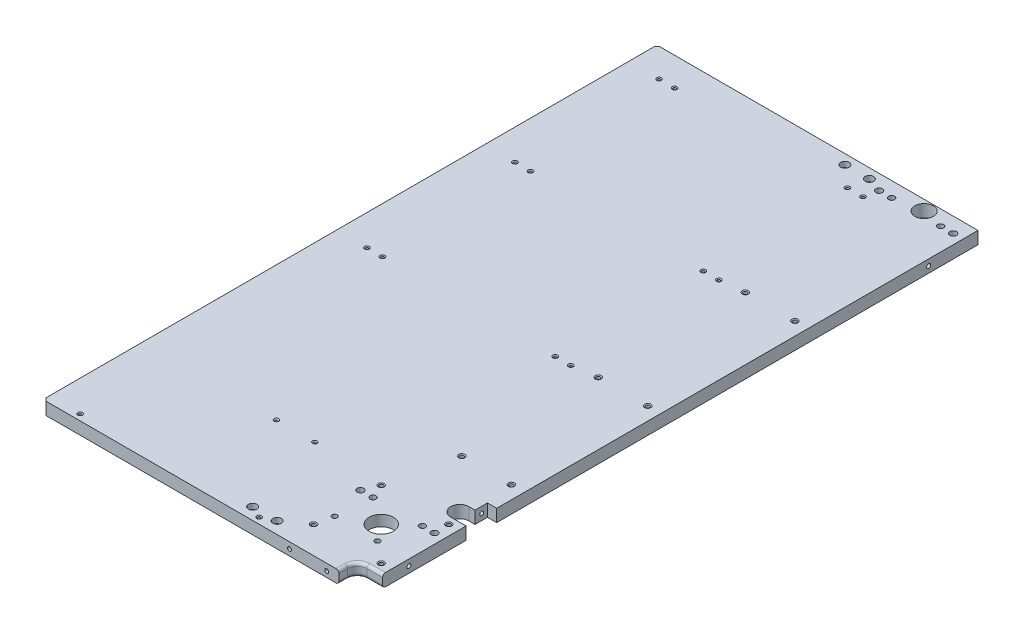
SolidWorks part; units mm, degrees
material "1060 Alloy"
ref_plane "Front Plane" through (0, 0, 0) normal (0, 0, 1) x (1, 0, 0)
ref_plane "Top Plane" through (0, 0, 0) normal (0, 1, 0) x (1, 0, 0)
ref_plane "Right Plane" through (0, 0, 0) normal (1, 0, 0) x (0, 0, -1)
sketch "Sketch1" plane through (0, 0, 0) normal (0, 1, 0) x (1, 0, 0)
  line L1 (0, 632) -> (330.5, 632)
  line L2 (0, 632) -> (0, 0)
  line L3 (0, 0) -> (330.5, 0)
  line L4 (330.5, 632) -> (330.5, 0)
  dimension "D1" = 632
  dimension "D2" = 330.5
extrude "Boss-Extrude1" add sketch "Sketch1" along normal blind 12.8
sketch "Sketch2" plane through (0, 12.8, 0) normal (0, 1, 0) x (-1, 0, 0)
  line L0 (-330.5, 0) -> (-330.5, -632) construction
  line L1 (-330.5, 0) -> (-304.5, 0)
  line L2 (-330.5, 0) -> (-330.5, -19)
  line L3 (-330.5, -19) -> (-314.5, -19)
  line L4 (-304.5, 0) -> (-304.5, -9)
  line L5 (-330.5, -136.5) -> (-320.95, -136.5)
  line L6 (-330.5, -136.5) -> (-330.5, -105)
  line L7 (-330.5, -105) -> (-314.68, -105)
  line L8 (-320.95, -136.5) -> (-320.95, -123.7)
  line L9 (-320.95, -123.7) -> (-314.68, -123.7)
  line L10 (-305.33, -114.35) -> (-305.33, 515.3854) construction
  line L11 (0, 0) -> (-330.5, 0) construction
  arc A0 (-304.5, -9) -> (-314.5, -19) centre (-314.5, -9) cw
  arc A1 (-314.68, -105) -> (-314.68, -123.7) centre (-314.68, -114.35) cw
  dimension "D1" = 10
  dimension "D2" = 19
  dimension "D3" = 26
  dimension "D4" = 31.5
  dimension "D5" = 18.7
  dimension "D6" = 9.55
  dimension "D7" = 25.17
  dimension "D8" = 105
extrude "Cut-Extrude1" cut sketch "Sketch2" against normal through all
fillet "Fillet1" radius 3 6 edges at (304.5, 0, -4.5) (307.4289, 0, -16.0711) (304.5, 12.8, -4.5) (307.4289, 12.8, -16.0711) (322.5, 0, -19) (322.5, 12.8, -19)
sketch "Sketch3" plane through (0, 12.8, 0) normal (0, 1, 0) x (-1, 0, 0)
  line L0 (0, -6.3) -> (-286.561, -6.3) construction
  line L1 (0, -632) -> (0, 0) construction
  line L2 (0, -302) -> (-330.5, -302) construction
  line L3 (0, -454.4) -> (-330.5, -454.4) construction
  line L4 (0, -602.8) -> (-330.5, -602.8) construction
  line L5 (0, 0) -> (-301.5, 0) construction
  line L7 (-31.4, -302) -> (-31.4, -602.8) construction
  line L8 (-47.4, -302) -> (-47.4, -602.8) construction
  line L9 (-225.3, -302) -> (-225.3, -602.8) construction
  line L10 (-241.3, -302) -> (-241.3, -602.8) construction
  line L11 (-330.5, -136.5) -> (-330.5, -632) construction
  circle A0 centre (-31.8, -6.3) radius 1.45
  circle A1 centre (-216.1, -6.3) radius 1.45
  circle A2 centre (-31.4, -302) radius 1.45
  circle A3 centre (-47.4, -302) radius 1.45
  circle A4 centre (-31.4, -454.4) radius 1.45
  circle A5 centre (-47.4, -454.4) radius 1.45
  circle A6 centre (-31.4, -602.8) radius 1.45
  circle A7 centre (-47.4, -602.8) radius 1.45
  circle A8 centre (-225.3, -602.8) radius 1.45
  circle A9 centre (-241.3, -602.8) radius 1.45
  circle A10 centre (-225.3, -454.4) radius 1.45
  circle A11 centre (-241.3, -454.4) radius 1.45
  circle A12 centre (-241.3, -302) radius 1.45
  circle A13 centre (-225.3, -302) radius 1.45
  dimension "D2" = 2.9
  dimension "D1" = 6.3
  dimension "D3" = 31.8
  dimension "D4" = 216.1
  dimension "D5" = 302
  dimension "D6" = 454.4
  dimension "D7" = 602.8
  dimension "D8" = 31.4
  dimension "D9" = 47.4
  dimension "D10" = 225.3
  dimension "D11" = 241.3
extrude "Cut-Extrude2" cut sketch "Sketch3" against normal through all
chamfer "Chamfer1" distance 1 angle 30 28 edges at (31.8, 0, -4.85) (216.1, 0, -4.85) (31.4, 0, -300.55) (47.4, 0, -300.55) (225.3, 0, -300.55) (241.3, 0, -300.55) (241.3, 0, -601.35) (47.4, 0, -601.35) (47.4, 0, -452.95) (31.4, 0, -452.95) (241.3, 0, -452.95) (225.3, 0, -452.95) (31.4, 0, -601.35) (225.3, 0, -601.35) (241.3, 12.8, -601.35) (225.3, 12.8, -601.35) (31.4, 12.8, -601.35) (47.4, 12.8, -601.35) (47.4, 12.8, -300.55) (31.4, 12.8, -452.95) (47.4, 12.8, -452.95) (241.3, 12.8, -452.95) (225.3, 12.8, -452.95) (241.3, 12.8, -300.55) (225.3, 12.8, -300.55) (216.1, 12.8, -4.85) (31.8, 12.8, -4.85) (31.4, 12.8, -300.55)
sketch "Sketch4" plane through (0, 12.8, 0) normal (0, 1, 0) x (-1, 0, 0)
  line L0 (0, -305.5) -> (-330.5, -305.5) construction
  line L1 (0, -632) -> (0, 0) construction
  line L2 (-330.5, -136.5) -> (-330.5, -632) construction
  line L3 (0, -457) -> (-330.5, -457) construction
  line L4 (0, -165.1) -> (-330.5, -165.1) construction
  line L5 (-266, -457) -> (-266, -165.1) construction
  line L6 (-317, -457) -> (-317, -165.1) construction
  line L7 (0, 0) -> (-301.5, 0) construction
  circle A0 centre (-266, -457) radius 2.1
  circle A1 centre (-317, -457) radius 2.1
  circle A2 centre (-266, -305.5) radius 2.1
  circle A3 centre (-317, -305.5) radius 2.1
  circle A4 centre (-266, -165.1) radius 2.1
  circle A5 centre (-317, -165.1) radius 2.1
  dimension "D1" = 4.2
  dimension "D2" = 266
  dimension "D3" = 317
  dimension "D4" = 165.1
  dimension "D5" = 305.5
  dimension "D6" = 457
extrude "Cut-Extrude3" cut sketch "Sketch4" against normal through all
chamfer "Chamfer2" distance 1 angle 30 12 edges at (266, 0, -454.9) (317, 0, -454.9) (266, 0, -303.4) (317, 0, -303.4) (266, 0, -163) (317, 0, -163) (317, 12.8, -163) (266, 12.8, -163) (266, 12.8, -303.4) (317, 12.8, -303.4) (317, 12.8, -454.9) (266, 12.8, -454.9)
sketch "Sketch5" plane through (0, 12.8, 0) normal (0, 1, 0) x (1, 0, 0)
  line L0 (250.5, 28) -> (320.1, 97.6) construction
  line L1 (250.5, 97.6) -> (320.1, 97.6) construction
  line L2 (250.5, 97.6) -> (250.5, 28) construction
  line L3 (250.5, 28) -> (320.1, 28) construction
  line L4 (320.1, 97.6) -> (320.1, 28) construction
  line L5 (0, 0) -> (301.5, 0) construction
  line L7 (0, 632) -> (0, 0) construction
  circle A0 centre (285.3, 62.8) radius 12.5
  circle A1 centre (320.1, 97.6) radius 2.1
  circle A2 centre (320.1, 28) radius 2.1
  circle A3 centre (250.5, 28) radius 2.1
  circle A4 centre (250.5, 97.6) radius 2.1
  dimension "D1" = 25
  dimension "D2" = 4.2
  dimension "D3" = 69.6
  dimension "D4" = 28
  dimension "D5" = 250.5
extrude "Cut-Extrude4" cut sketch "Sketch5" against normal through all
sketch "Sketch6" plane through (0, 0, 0) normal (0, -1, 0) x (1, 0, 0)
  circle A0 centre (285.3, -62.8) radius 36.425
  dimension "D1" = 72.85
extrude "Cut-Extrude5" cut sketch "Sketch6" against normal blind 1.7
chamfer "Chamfer3" distance 1 angle 30 8 edges at (250.5, 0, -25.9) (320.1, 0, -95.5) (250.5, 0, -95.5) (320.1, 0, -25.9) (250.5, 12.8, -25.9) (320.1, 12.8, -25.9) (320.1, 12.8, -95.5) (250.5, 12.8, -95.5)
sketch "Sketch7" plane through (0, 12.8, 0) normal (0, 1, 0) x (1, 0, 0)
  line L0 (254.2, 45.9) -> (330.5, 45.9) construction
  line L1 (330.5, 22) -> (330.5, 105) construction
  line L2 (0, 0) -> (301.5, 0) construction
  line L3 (0, 632) -> (0, 0) construction
  line L4 (330.5, 82.5) -> (0, 82.5) construction
  circle A0 centre (254.2, 45.9) radius 2.7
  circle A1 centre (298.4, 45.9) radius 2.7
  circle A2 centre (308, 82.5) radius 3.1
  circle A3 centre (257.2, 82.5) radius 3.1
  circle A4 centre (320.5, 82.5) radius 3.425
  circle A5 centre (244.2, 82.5) radius 3.425
  dimension "D4" = 5.4
  dimension "D7" = 6.2
  dimension "D8" = 6.85
  dimension "D1" = 45.9
  dimension "D2" = 254.2
  dimension "D3" = 298.4
  dimension "D5" = 257.2
  dimension "D6" = 82.5
  dimension "D9" = 244.2
  dimension "D10" = 308
  dimension "D11" = 320.5
extrude "Cut-Extrude6" cut sketch "Sketch7" against normal through all
sketch "Sketch13" plane through (0, 0, 0) normal (0, -1, 0) x (1, 0, 0)
  circle A0 centre (254.2, -45.9) radius 4.4
  circle A1 centre (298.4, -45.9) radius 4.4
  dimension "D1" = 8.8
extrude "Cut-Extrude12" cut sketch "Sketch13" against normal blind 6.76
sketch "Sketch8" plane through (0, 12.8, 0) normal (0, 1, 0) x (1, 0, 0)
  line L0 (330.5, 621.5) -> (0, 621.5) construction
  line L1 (330.5, 136.5) -> (330.5, 632) construction
  line L2 (0, 632) -> (0, 0) construction
  line L4 (0, 0) -> (301.5, 0) construction
  line L6 (276, 621.5) -> (276, 590.9853) construction
  circle A0 centre (285.51, 621.5) radius 9.51
  dimension "D2" = 19.02
  dimension "D1" = 621.5
  dimension "D3" = 276
extrude "Cut-Extrude7" cut sketch "Sketch8" against normal through all
sketch "Sketch9" plane through (0, 12.8, 0) normal (0, 1, 0) x (-1, 0, 0)
  line L0 (-239.5297, -622) -> (-164.9722, -622) construction
  line L1 (0, -12.25) -> (-330.5, -12.25) construction
  line L2 (0, -632) -> (0, 0) construction
  line L3 (0, 0) -> (-301.5, 0) construction
  line L4 (-330.5, -12.25) -> (-330.5, -42.1724) construction
  line L5 (-330.5, -22) -> (-330.5, -105) construction
  line L6 (-203.5, -622) -> (-203.5, -12.25) construction
  line L7 (-228.7, -622) -> (-228.7, -12.25) construction
  circle A0 centre (-228.7, -622) radius 2.6
  circle A1 centre (-203.5, -622) radius 2.6
  circle A2 centre (-203.5, -12.25) radius 2.6
  circle A3 centre (-228.7, -12.25) radius 2.6
  dimension "D4" = 5.2
  dimension "D1" = 622
  dimension "D2" = 203.5
  dimension "D3" = 228.7
  dimension "D5" = 12.25
extrude "Cut-Extrude8" cut sketch "Sketch9" against normal through all
sketch "Sketch10" plane through (0, 12.8, 0) normal (0, 1, 0) x (-1, 0, 0)
  line L3 (-330.5, -12.25) -> (-330.5, -22) construction
  circle A0 centre (-203.5, -622) radius 4.365
  circle A1 centre (-228.7, -622) radius 4.365
  circle A2 centre (-203.5, -12.25) radius 4.365
  circle A3 centre (-228.7, -12.25) radius 4.365
  circle A4 centre (-203.5, -12.25) radius 2.6 construction
  circle A5 centre (-228.7, -12.25) radius 2.6 construction
  dimension "D1" = 8.73
extrude "Cut-Extrude9" cut sketch "Sketch10" against normal blind 5.58
sketch "Sketch11" plane through (0, 12.8, 0) normal (0, 1, 0) x (-1, 0, 0)
  line L0 (0, -616.5) -> (-330.5, -616.5) construction
  line L3 (0, -632) -> (0, 0) construction
  line L4 (-330.5, -136.5) -> (-330.5, -632) construction
  line L7 (-330.5, -632) -> (0, -632) construction
  circle A0 centre (-244.2, -616.5) radius 3.425
  circle A1 centre (-257, -616.5) radius 3.1
  circle A2 centre (-307.5, -616.5) radius 3.1
  circle A3 centre (-320.5, -616.5) radius 3.425
  dimension "D2" = 6.85
  dimension "D1" = 6.2
  dimension "D3" = 15.5
  dimension "D4" = 244.2
  dimension "D5" = 257
  dimension "D6" = 307.5
  dimension "D7" = 320.5
extrude "Cut-Extrude10" cut sketch "Sketch11" against normal through all
sketch "Sketch12" plane through (0, 0, 0) normal (0, -1, 0) x (1, 0, 0)
  circle A0 centre (244.2, -616.5) radius 6.15
  circle A1 centre (320.5, -616.5) radius 6.15
  circle A2 centre (320.5, -82.5) radius 6.15
  circle A3 centre (244.2, -82.5) radius 6.15
  dimension "D1" = 12.3
extrude "Cut-Extrude11" cut sketch "Sketch12" against normal blind 7.82
sketch "Sketch15" plane through (0, 12.8, 0) normal (0, 1, 0) x (1, 0, 0)
  line L0 (330.5, 101.9) -> (0, 101.9) construction
  line L1 (330.5, 22) -> (330.5, 105) construction
  line L2 (0, 632) -> (0, 0) construction
  line L3 (0, 0) -> (301.5, 0) construction
  circle A0 centre (138.3, 101.9) radius 1.35
  circle A1 centre (177.9, 101.9) radius 1.35
  dimension "D4" = 2.7
  dimension "D1" = 101.9
  dimension "D2" = 138.3
  dimension "D3" = 177.9
extrude "Cut-Extrude13" cut sketch "Sketch15" against normal through all
chamfer "Chamfer4" distance 1 angle 45 4 edges at (177.9, 0, -100.55) (138.3, 0, -100.55) (177.9, 12.8, -100.55) (138.3, 12.8, -100.55)
sketch "Sketch16" plane through (0, 0, 0) normal (0, 0, 1) x (1, 0, 0)
  line L0 (0, 6.4) -> (304.5, 6.4) construction
  line L1 (0, 12.8) -> (0, 0) construction
  line L2 (304.5, 3) -> (304.5, 9.8) construction
  line L3 (292, 12.8) -> (292, 0) construction
  line L4 (0, 12.8) -> (301.5, 12.8) construction
  line L5 (0, 0) -> (301.5, 0) construction
  line L6 (253.7, 12.8) -> (253.7, 0) construction
  circle A0 centre (253.7, 6.4) radius 2.025
  circle A1 centre (292, 5.8) radius 2.025
  dimension "D2" = 4.05
  dimension "D1" = 5.8
  dimension "D3" = 253.7
  dimension "D4" = 292
extrude "Cut-Extrude14" cut sketch "Sketch16" against normal blind 14.56
sketch "Sketch17" plane through (330.5, 0, 0) normal (1, 0, 0) x (0, 0, -1)
  line L0 (632, 6.4) -> (0, 6.4) construction
  line L1 (632, 12.8) -> (632, 0) construction
  line L2 (0, 0) -> (0, 6.4) construction
  circle A0 centre (46.12, 6.4) radius 2.03
  circle A1 centre (130.62, 6.4) radius 2.03
  circle A2 centre (581.2, 6.4) radius 2.13
  dimension "D3" = 4.06
  dimension "D4" = 4.06
  dimension "D5" = 4.26
  dimension "D1" = 46.12
  dimension "D2" = 130.62
  dimension "D6" = 581.2
  dimension "D7" = 50.8
extrude "Cut-Extrude15" cut sketch "Sketch17" against normal blind 15.24 contours A0 | A2
sketch "Sketch18" plane through (320.95, 0, 0) normal (1, 0, 0) x (0, 0, -1)
  circle A0 centre (130.62, 6.4) radius 2.03 construction
  circle A1 centre (130.62, 6.4) radius 2.03
extrude "Cut-Extrude17" cut sketch "Sketch18" against normal blind 15.24
sketch "Sketch19" plane through (0, 0, -632) normal (0, 0, -1) x (-1, 0, 0)
  line L0 (0, 6.4) -> (-330.5, 6.4) construction
  line L1 (-330.5, 12.8) -> (-330.5, 0) construction
  line L2 (0, 12.8) -> (0, 0) construction
  circle A0 centre (-215.95, 6.4) radius 1.475
  circle A1 centre (-38.1, 6.4) radius 1.475
  dimension "D3" = 2.95
  dimension "D1" = 215.95
  dimension "D2" = 38.1
chamfer "Chamfer5" distance 3 2 edges at (0, 6.4, 0) (0, 6.4, -632)
extrude "Cut-Extrude18" cut sketch "Sketch19" against normal blind 15.24
chamfer "Chamfer6" distance 1 angle 45 2 edges at (36.625, 6.4, -632) (214.475, 6.4, -632)
